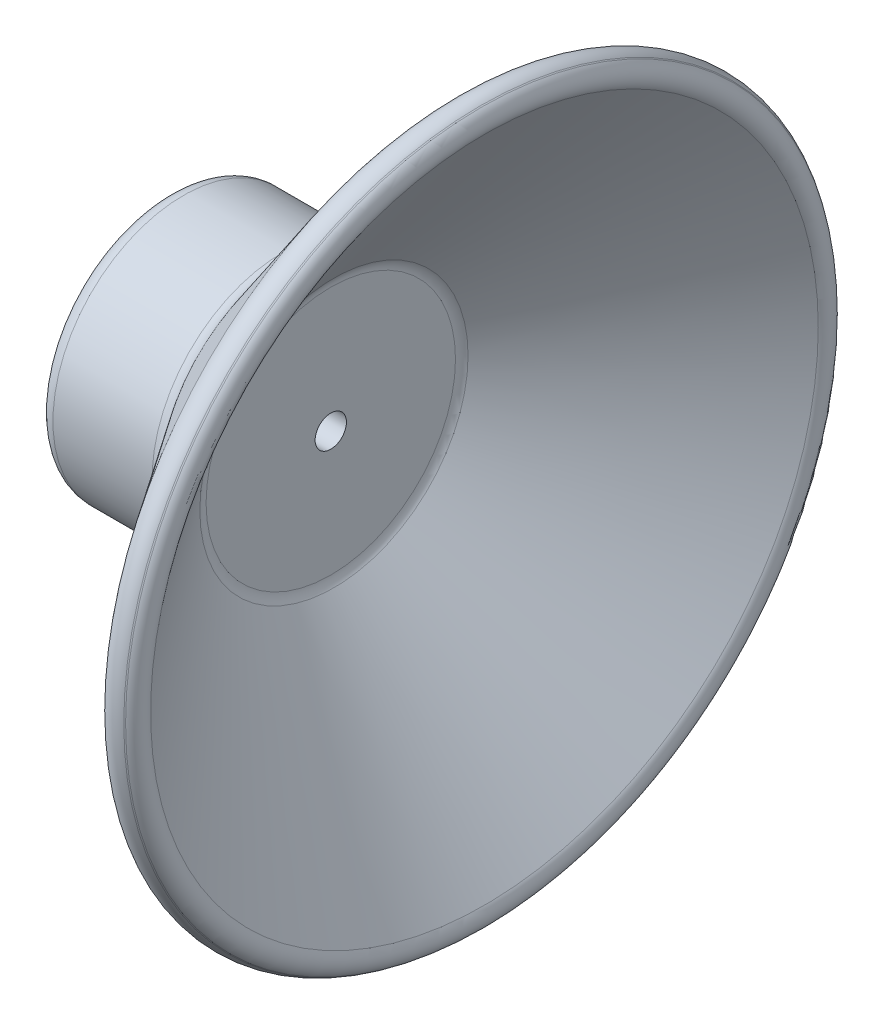
SolidWorks part; units mm, degrees
ref_plane "Front Plane" through (0, 0, 0) normal (0, 0, 1) x (1, 0, 0)
ref_plane "Top Plane" through (0, 0, 0) normal (0, 1, 0) x (1, 0, 0)
ref_plane "Right Plane" through (0, 0, 0) normal (1, 0, 0) x (0, 0, -1)
sketch "Sketch2" plane through (0, 0, 0) normal (0, 1, 0) x (1, 0, 0)
  line L0 (-17.337, 11.049) -> (-17.337, 11.176)
  line L1 (-15.813, 12.7) -> (-6.161, 12.7)
  line L2 (-4.9438, 13.3068) -> (10.9602, 34.4122)
  line L3 (13.0945, 34.7122) -> (13.1959, 34.6357)
  line L4 (13.4959, 32.5015) -> (-1.1551, 13.059)
  line L5 (-1.462, 12.1418) -> (-1.462, 0)
  line L6 (-1.462, 0) -> (-4.637, 0)
  line L7 (-4.637, 0) -> (-4.637, 8.001)
  line L8 (-6.161, 9.525) -> (-15.813, 9.525)
  arc A0 (-1.1551, 13.059) -> (-1.462, 12.1418) centre (0.062, 12.1418) ccw
  arc A1 (-6.161, 12.7) -> (-4.9438, 13.3068) centre (-6.161, 14.224) ccw
  arc A2 (10.9602, 34.4122) -> (13.0945, 34.7122) centre (12.1773, 33.495) cw
  arc A3 (13.1959, 34.6357) -> (13.4959, 32.5015) centre (12.2788, 33.4186) cw
  arc A4 (-17.337, 11.049) -> (-15.813, 9.525) centre (-15.813, 11.049) ccw
  arc A5 (-17.337, 11.176) -> (-15.813, 12.7) centre (-15.813, 11.176) cw
  arc A6 (-4.637, 8.001) -> (-6.161, 9.525) centre (-6.161, 8.001) ccw
  point P3 (-10.987, 12.7)
  point P19 (14.413, 33.7186)
  point P26 (-2.469, 12.7)
  point P27 (1.5688, 12.0095)
  point P28 (-0.8838, 9.9448)
  point P29 (0, 0)
  point P30 (-4.9082, 14.224)
  point P31 (0, 0)
  point P32 (0, 0)
  dimension "D7" = 1.524
  dimension "D8" = 1.524
  dimension "D1" = 3.175
  dimension "D2" = 3.175
  dimension "D3" = 3.175
  dimension "D4" = 9.525
  dimension "D5" = 12.7
  dimension "D6" = 31.75
  dimension "D9" = 12.7
  dimension "D10" = 127
revolve "Revolve1" add sketch "Sketch2" angle 360 about L6
sketch "Sketch3" plane through (-4.637, 0, 0) normal (-1, 0, 0) x (0, 0, 1)
  circle A0 centre (0, 0) radius 1.524
  dimension "D1" = 3.048
extrude "Cut-Extrude1" cut sketch "Sketch3" against normal through all
